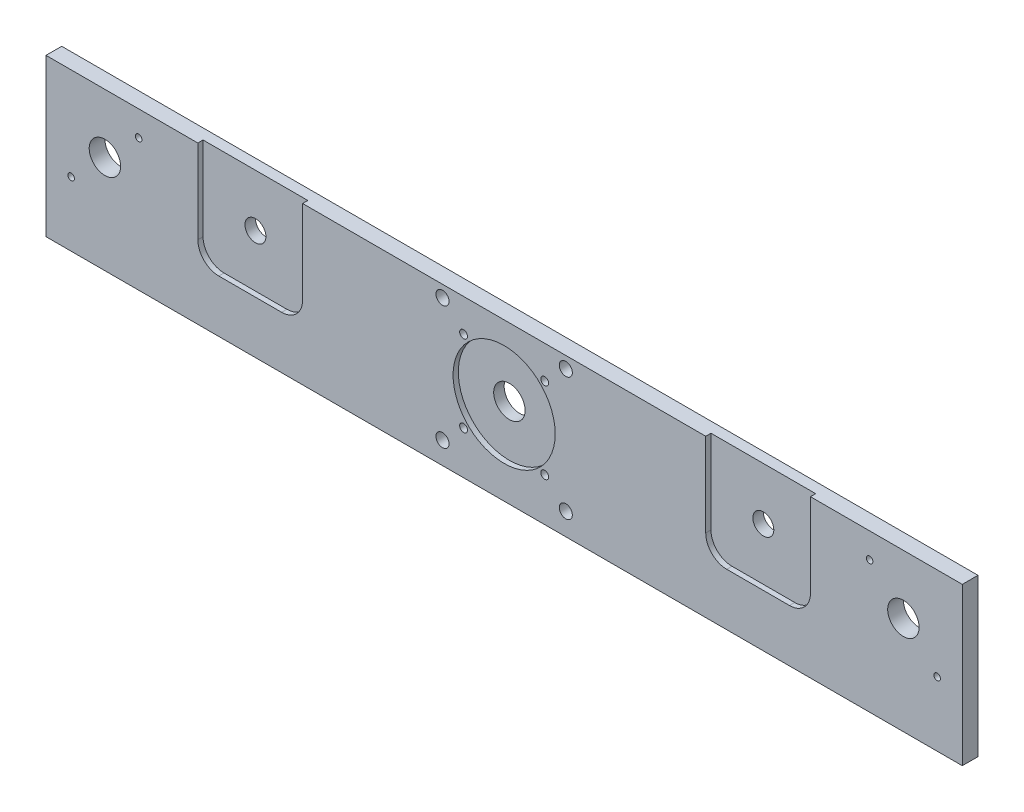
SolidWorks part; units mm, degrees
ref_plane "Alzado" through (0, 0, 0) normal (0, 0, 1) x (1, 0, 0)
ref_plane "Planta" through (0, 0, 0) normal (0, 1, 0) x (1, 0, 0)
ref_plane "Vista lateral" through (0, 0, 0) normal (1, 0, 0) x (0, 0, -1)
sketch "Croquis1" plane through (0, 0, 0) normal (0, 0, 1) x (1, 0, 0)
  line L1 (-350, -60) -> (0, -60)
  line L2 (-350, -60) -> (-350, 0)
  line L3 (-350, 0) -> (0, 0)
  line L4 (0, -60) -> (0, 0)
  dimension "D1" = 350
  dimension "D2" = 60
extrude "Saliente-Extruir1" add sketch "Croquis1" along normal blind 6 contours L3 L4 L1 L2
sketch "Croquis2" plane through (0, 0, 6) normal (0, 0, 1) x (1, 0, 0)
  line L0 (-350, -60) -> (-350, 0) construction
  line L1 (0, -60) -> (0, 0) construction
  line L2 (-350, -60) -> (0, -60) construction
  line L3 (-340.4047, -35.4047) -> (-314.5953, -9.5953) construction
  line L4 (-35.4047, -9.5953) -> (-9.5953, -35.4047) construction
  line L5 (-350, 0) -> (0, 0) construction
  circle A0 centre (-327.5, -22.5) radius 6
  circle A1 centre (-22.5, -22.5) radius 6
  circle A2 centre (-327.5, -22.5) radius 18.25 construction
  circle A4 centre (-314.5953, -9.5953) radius 1.25
  circle A5 centre (-340.4047, -35.4047) radius 1.25
  circle A6 centre (-22.5, -22.5) radius 18.25 construction
  circle A7 centre (-35.4047, -9.5953) radius 1.25
  circle A8 centre (-9.5953, -35.4047) radius 1.25
  circle A9 centre (-22.5, -22.5) radius 21 construction
  circle A10 centre (-327.5, -22.5) radius 21 construction
  dimension "D1" = 12
  dimension "D2" = 12
  dimension "D7" = 36.5
  dimension "D9" = 2.5
  dimension "D10" = 2.5
  dimension "D11" = 36.5
  dimension "D13" = 2.5
  dimension "D14" = 2.5
  dimension "D15" = 42
  dimension "D16" = 42
  dimension "D3" = 22.5
  dimension "D4" = 22.5
  dimension "D5" = 22.5
  dimension "D6" = 22.5
  dimension "D8" = 45
  dimension "D12" = 45
extrude "Cortar-Extruir1" cut sketch "Croquis2" against normal through all
sketch "Croquis3" plane through (0, 0, 6) normal (0, 0, 1) x (1, 0, 0)
  line L3 (-198.55, -51.55) -> (-151.45, -51.55) construction
  line L6 (-198.55, -51.55) -> (-198.55, -4.45) construction
  line L9 (-350, 0) -> (0, 0) construction
  line L10 (-198.55, -4.45) -> (-151.45, -4.45) construction
  line L13 (-151.45, -51.55) -> (-151.45, -4.45) construction
  line L16 (-198.55, -51.55) -> (-151.45, -4.45) construction
  line L21 (-198.55, -4.45) -> (-151.45, -51.55) construction
  line L24 (-190.5, -43.5) -> (-159.5, -43.5) construction
  line L27 (-190.5, -43.5) -> (-190.5, -12.5) construction
  line L30 (-190.5, -12.5) -> (-159.5, -12.5) construction
  line L34 (0, -60) -> (0, 0) construction
  line L35 (-159.5, -43.5) -> (-159.5, -12.5) construction
  line L36 (-190.5, -43.5) -> (-159.5, -12.5) construction
  line L37 (-190.5, -12.5) -> (-159.5, -43.5) construction
  circle A27 centre (-175, -28) radius 6
  circle A28 centre (-190.5, -12.5) radius 1.5
  circle A29 centre (-159.5, -12.5) radius 1.5
  circle A30 centre (-190.5, -43.5) radius 1.5
  circle A31 centre (-151.45, -51.55) radius 2.5
  circle A32 centre (-198.55, -51.55) radius 2.5
  circle A33 centre (-159.5, -43.5) radius 1.5
  circle A34 centre (-151.45, -4.45) radius 2.5
  circle A35 centre (-198.55, -4.45) radius 2.5
  dimension "D5" = 3
  dimension "D9" = 31
  dimension "D41" = 12
  dimension "D1" = 3
  dimension "D2" = 3
  dimension "D3" = 5
  dimension "D10" = 5
  dimension "D11" = 5
  dimension "D12" = 5
  dimension "D13" = 3
  dimension "D6" = 47.1
  dimension "D7" = 47.1
  dimension "D8" = 31
  dimension "D42" = 175
  dimension "D43" = 28
extrude "Cortar-Extruir2" cut sketch "Croquis3" against normal through all
sketch "Croquis5" plane through (0, 0, 6) normal (0, 0, 1) x (1, 0, 0)
  line L0 (-350, 0) -> (0, 0) construction
  line L1 (-292, 0) -> (-252, 0)
  line L2 (-292, 0) -> (-292, -32)
  line L3 (-284, -40) -> (-260, -40)
  line L4 (-252, 0) -> (-252, -32)
  line L5 (-350, -60) -> (-350, 0) construction
  line L6 (-98, 0) -> (-58, 0)
  line L7 (-98, 0) -> (-98, -32)
  line L8 (-90, -40) -> (-66, -40)
  line L9 (-58, 0) -> (-58, -32)
  line L10 (0, -60) -> (0, 0) construction
  arc A0 (-260, -40) -> (-252, -32) centre (-260, -32) ccw
  arc A1 (-284, -40) -> (-292, -32) centre (-284, -32) cw
  arc A2 (-66, -40) -> (-58, -32) centre (-66, -32) ccw
  arc A3 (-90, -40) -> (-98, -32) centre (-90, -32) cw
  circle A4 centre (-175, -28) radius 19.5
  point P11 (-252, -40)
  dimension "D4" = 8
  dimension "D6" = 8
  dimension "D9" = 39
  dimension "D1" = 40
  dimension "D2" = 58
  dimension "D3" = 40
  dimension "D5" = 40
  dimension "D7" = 58
  dimension "D8" = 40
extrude "Cortar-Extruir4" cut sketch "Croquis5" against normal blind 2
sketch "Croquis7" plane through (0, 0, 4) normal (0, 0, 1) x (1, 0, 0)
  line L0 (-252, -32) -> (-252, 0) construction
  line L1 (-252, 0) -> (-292, 0) construction
  line L3 (-58, -32) -> (-58, 0) construction
  line L4 (-58, 0) -> (-98, 0) construction
  circle A0 centre (-272, -20) radius 4
  circle A1 centre (-78, -20) radius 4
  dimension "D1" = 8
  dimension "D4" = 8
  dimension "D5" = 20
  dimension "D2" = 20
  dimension "D3" = 20
  dimension "D6" = 20
extrude "Cortar-Extruir5" cut sketch "Croquis7" against normal through all
